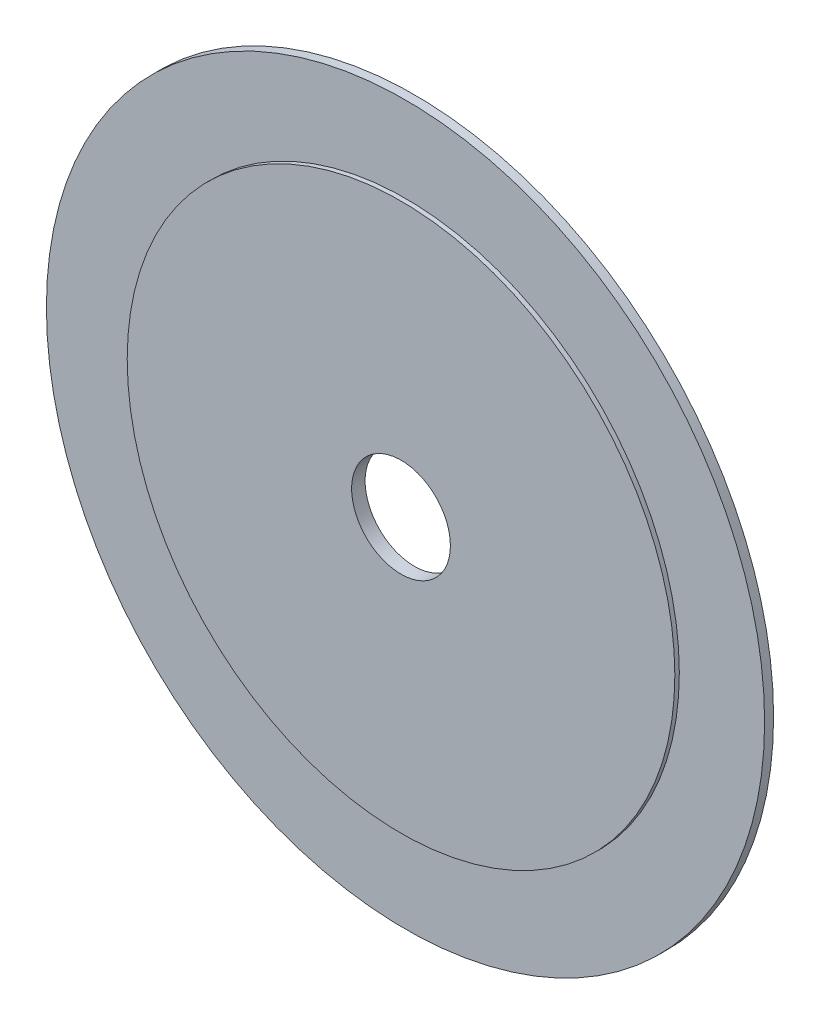
SolidWorks part; units mm, degrees
material "1.0116 (S235J2G3)"
ref_plane "Front Plane" through (0, 0, 0) normal (0, 0, 1) x (1, 0, 0)
ref_plane "Top Plane" through (0, 0, 0) normal (0, 1, 0) x (1, 0, 0)
ref_plane "Right Plane" through (0, 0, 0) normal (1, 0, 0) x (0, 0, -1)
sketch "Sketch1" plane through (0, 0, 0) normal (0, 0, 1) x (1, 0, 0)
  circle A0 centre (0, 0) radius 80
  circle A1 centre (0, 0) radius 11
  dimension "D1" = 160
  dimension "D2" = 22
extrude "Boss-Extrude1" add sketch "Sketch1" along normal blind 3
sketch "Sketch2" plane through (0, 0, 3) normal (0, 0, 1) x (1, 0, 0)
  circle A0 centre (0, 0) radius 61
  dimension "D1" = 122
extrude "Cut-Extrude1" cut sketch "Sketch2" against normal blind 1 from surface at 0 flip side to cut contours A0 starting at face at (80, 0, 3)
